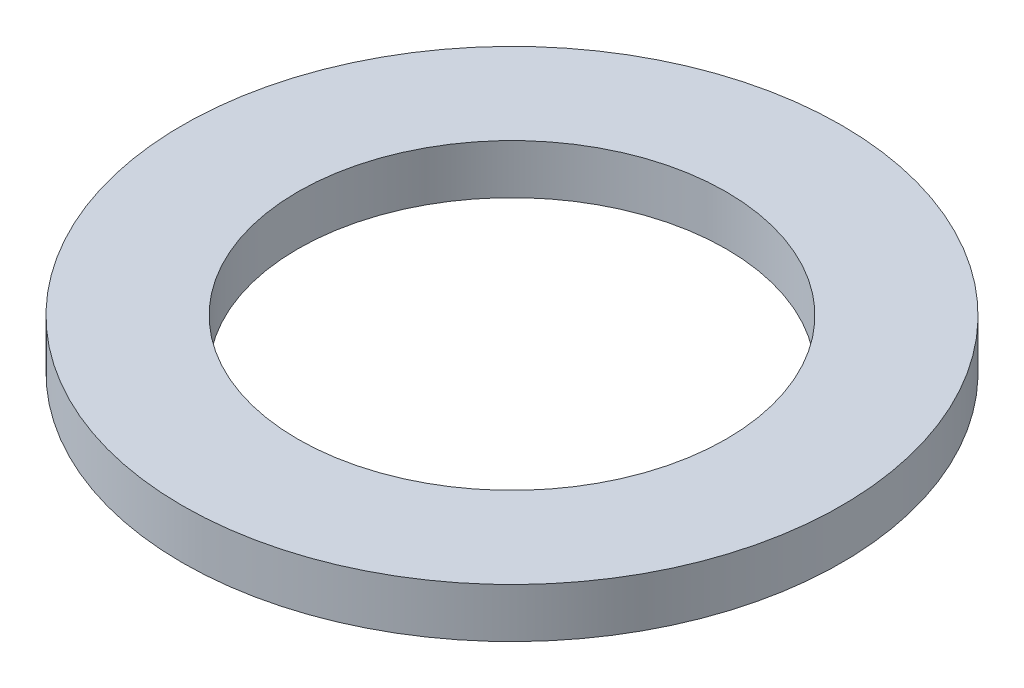
SolidWorks part; units mm, degrees
ref_plane "Front Plane" through (0, 0, 0) normal (0, 0, 1) x (1, 0, 0)
ref_plane "Top Plane" through (0, 0, 0) normal (0, 1, 0) x (1, 0, 0)
ref_plane "Right Plane" through (0, 0, 0) normal (1, 0, 0) x (0, 0, -1)
sketch "Sketch1" plane through (0, 0, 0) normal (0, 1, 0) x (1, 0, 0)
  circle A0 centre (0, 0) radius 13
  circle A1 centre (0, 0) radius 20
extrude "Boss-Extrude1" add sketch "Sketch1" along normal blind 3
